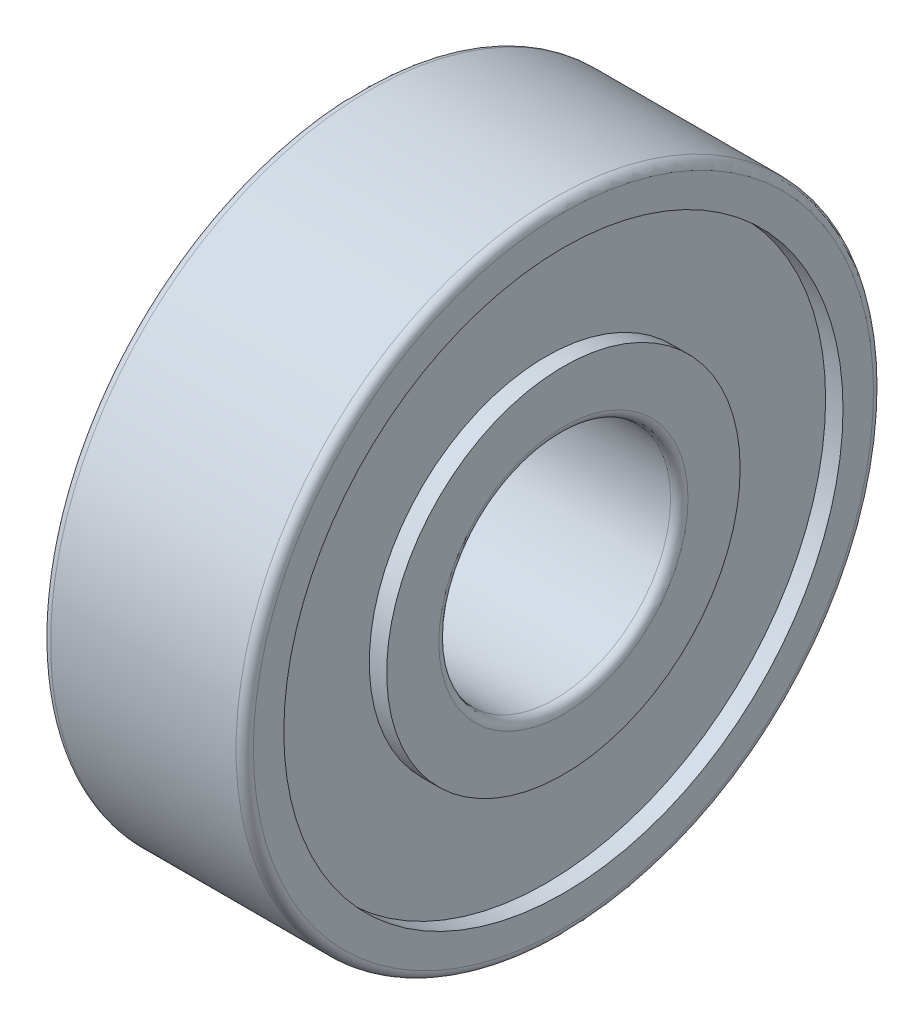
SolidWorks part; units mm, degrees
ref_plane "Front Plane" through (0, 0, 0) normal (0, 0, 1) x (1, 0, 0)
ref_plane "Top Plane" through (0, 0, 0) normal (0, 1, 0) x (1, 0, 0)
ref_plane "Right Plane" through (0, 0, 0) normal (1, 0, 0) x (0, 0, -1)
sketch "Sketch1" plane through (0, 0, 0) normal (0, 0, 1) x (1, 0, 0)
  line L0 (0.3, 4) -> (6.7, 4)
  line L1 (7, 4.3) -> (7, 6.1)
  line L2 (7, 6.1) -> (6.4, 6.1)
  line L3 (6.4, 6.1) -> (6.4, 9.65)
  line L4 (6.4, 9.65) -> (7, 9.65)
  line L5 (7, 9.65) -> (7, 10.7)
  line L6 (6.7, 11) -> (0.3, 11)
  line L7 (0, 10.7) -> (0, 9.65)
  line L8 (0, 9.65) -> (0.6, 9.65)
  line L9 (0.6, 9.65) -> (0.6, 6.1)
  line L10 (0.6, 6.1) -> (0, 6.1)
  line L11 (0, 6.1) -> (0, 4.3)
  line L12 (-0.0028, 0) -> (7.0028, 0) construction
  arc A0 (0, 4.3) -> (0.3, 4) centre (0.3, 4.3) ccw
  arc A1 (6.7, 4) -> (7, 4.3) centre (6.7, 4.3) ccw
  arc A2 (7, 10.7) -> (6.7, 11) centre (6.7, 10.7) ccw
  arc A3 (0.3, 11) -> (0, 10.7) centre (0.3, 10.7) ccw
revolve "Revolve1" add sketch "Sketch1" angle 360 about L12
